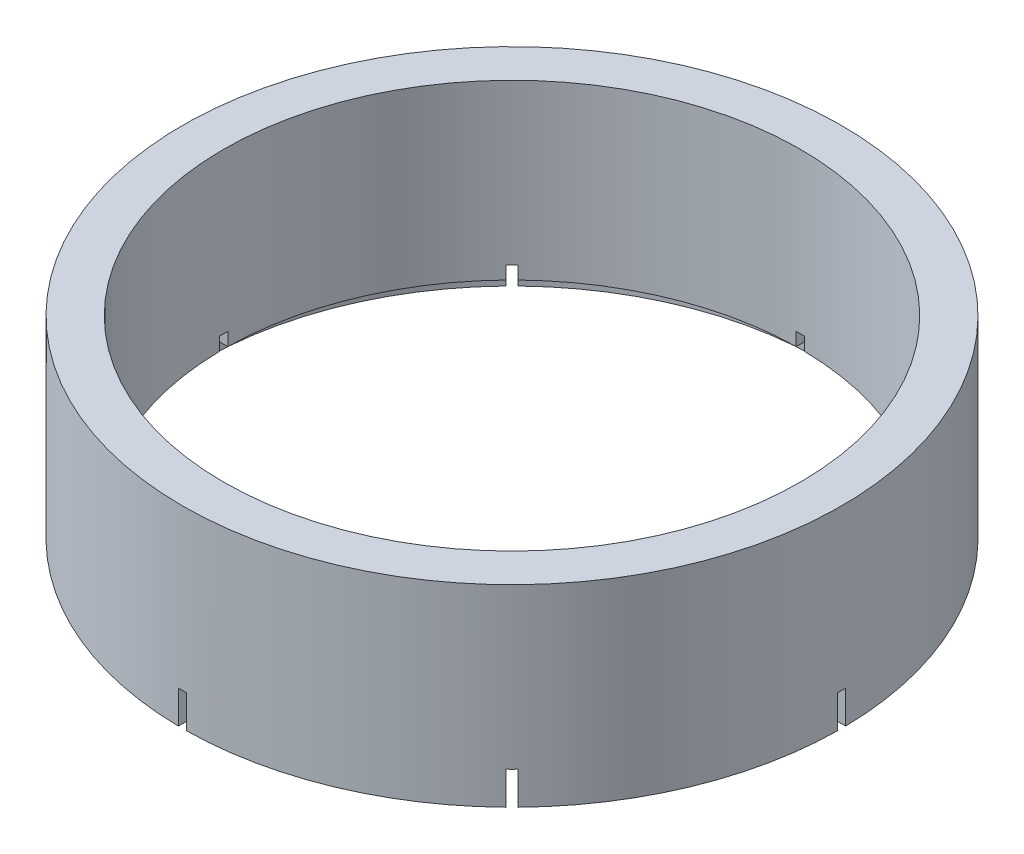
SolidWorks part; units mm, degrees
material "C (Graphite)"
ref_plane "Front Plane" through (0, 0, 0) normal (0, 0, 1) x (1, 0, 0)
ref_plane "Top Plane" through (0, 0, 0) normal (0, 1, 0) x (1, 0, 0)
ref_plane "Right Plane" through (0, 0, 0) normal (1, 0, 0) x (0, 0, -1)
sketch "Sketch1" plane through (0, 0, 0) normal (0, 1, 0) x (1, 0, 0)
  circle A0 centre (0, 0) radius 40
  circle A1 centre (0, 0) radius 35
  dimension "D1" = 80
  dimension "D2" = 70
extrude "Boss-Extrude1" add sketch "Sketch1" along normal blind 25.4
sketch "Sketch2" plane through (0, 0, 0) normal (0, -1, 0) x (1, 0, 0)
  circle A0 centre (0, 0) radius 37.5
  circle A1 centre (0, 0) radius 35
  dimension "D1" = 75
  dimension "D2" = 70
extrude "Cut-Extrude1" cut sketch "Sketch2" against normal blind 4.4
sketch "Sketch3" plane through (0, 0, 0) normal (0, 0, 1) x (1, 0, 0)
  line L0 (44, 0) -> (-44, 0) construction
  line L1 (-0.5, 0) -> (0.5, 0)
  line L2 (-0.5, 0) -> (-0.5, 6)
  line L3 (-0.5, 6) -> (0.5, 6)
  line L4 (0.5, 0) -> (0.5, 6)
  line L5 (0, -13.97) -> (0, 13.97) construction
  point P6 (0, 6)
  dimension "D1" = 0
  dimension "D2" = 1
  dimension "D3" = 6
extrude "Cut-Extrude2" cut sketch "Sketch3" against normal through all both and the other way through all
pattern_circular "CirPattern1" count 4 every 45 about axis through (0, 0, 0) along (0, 1, 0) of "Cut-Extrude2"
sketch "Sketch4" plane through (0, 0, 0) normal (0, -1, 0) x (1, 0, 0)
  circle A0 centre (0, 0) radius 45.8776
extrude "Cut-Extrude3" cut sketch "Sketch4" against normal blind 2
